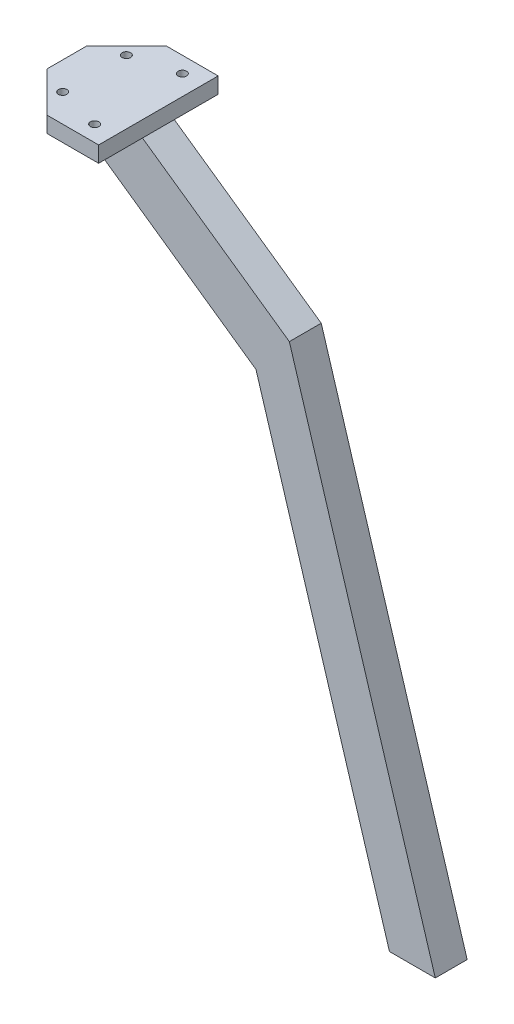
SolidWorks part; units mm, degrees
material "6061-T6 (SS)"
ref_plane "Front Plane" through (0, 0, 0) normal (0, 0, 1) x (1, 0, 0)
ref_plane "Top Plane" through (0, 0, 0) normal (0, 1, 0) x (1, 0, 0)
ref_plane "Right Plane" through (0, 0, 0) normal (1, 0, 0) x (0, 0, -1)
sketch "Sketch1" plane through (0, 0, 0) normal (0, 1, 0) x (1, 0, 0)
  line L0 (0, 20) -> (10, 30)
  line L1 (10, 0) -> (23, 0)
  line L2 (0, 10) -> (0, 20)
  line L3 (10, 30) -> (23, 30)
  line L4 (23, 0) -> (23, 30)
  line L6 (10, 0) -> (0, 10)
  circle A0 centre (6.9695, 7) radius 1.064
  circle A1 centre (18, 4) radius 1.064
  circle A2 centre (18, 26) radius 1.064
  circle A3 centre (6.9695, 23) radius 1.064
  dimension "D1" = 30
  dimension "D2" = 4
  dimension "D3" = 10
  dimension "D4" = 10
  dimension "D5" = 10
  dimension "D6" = 10
  dimension "D7" = 4
  dimension "D8" = 5
  dimension "D9" = 3
  dimension "D10" = 3
extrude "Boss-Extrude1" add sketch "Sketch1" along normal blind 4
ref_plane "Plane1" through (0, 0, -15) normal (0, 0, 1) x (1, 0, 0)
sketch "Sketch2" plane through (0, 0, -15) normal (0, 0, 1) x (1, 0, 0)
  line L0 (0, 0) -> (51.4862, -36.0511)
  line L2 (59.8618, -25.8109) -> (23, 0)
  line L3 (10, 0) -> (23, 0) construction
  line L4 (0, 0) -> (23, 0)
  line L5 (51.4862, -36.0511) -> (84.9853, -145.8109)
  line L6 (84.9853, -145.8109) -> (96.4862, -145.8109)
  line L7 (96.4862, -145.8109) -> (59.8618, -25.8109)
  dimension "D1" = 145
  dimension "D2" = 45
  dimension "D3" = 45
  dimension "D4" = 120
  dimension "D5" = 11
extrude "Boss-Extrude2" add sketch "Sketch2" along normal blind 4 and the other way blind 4
sketch "Sketch3" plane through (0, 4, 0) normal (0, 1, 0) x (1, 0, 0)
  line L0 (6.9695, 7) -> (6.9695, 23) construction
  point P4 (6.9695, 15)
equation "\"q0\"=6.15296"
